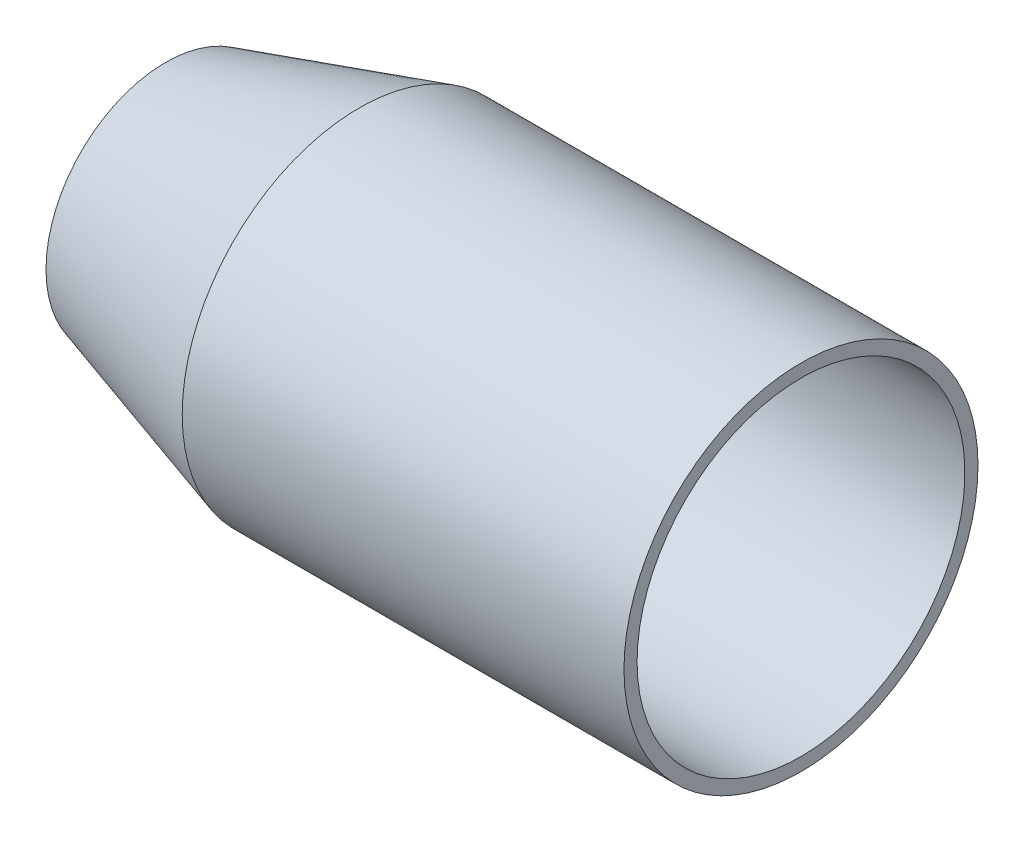
SolidWorks part; units mm, degrees
ref_plane "Front Plane" through (0, 0, 0) normal (0, 0, 1) x (1, 0, 0)
ref_plane "Top Plane" through (0, 0, 0) normal (0, 1, 0) x (1, 0, 0)
ref_plane "Right Plane" through (0, 0, 0) normal (1, 0, 0) x (0, 0, -1)
sketch "Sketch1" plane through (0, 0, 0) normal (0, 0, 1) x (1, 0, 0)
  line L0 (0, 0) -> (541.4119, 0) construction
  line L1 (266.7, 68.795) -> (266.7, 137.92)
  line L2 (266.7, 137.92) -> (239.01, 137.92)
  line L3 (239.01, 137.92) -> (239.01, 74.295)
  line L4 (239.01, 74.295) -> (81.28, 74.295)
  line L5 (239.01, 68.795) -> (82.0785, 68.795)
  line L6 (239.01, 68.795) -> (266.7, 68.795)
  line L7 (81.28, 74.295) -> (0, 50.1868)
  line L8 (82.0785, 68.795) -> (0, 44.45)
  line L9 (0, 50.1868) -> (0, 44.45)
  line L10 (239.01, 74.295) -> (266.7, 74.295)
  dimension "D2" = 27.69
  dimension "D3" = 74.295
  dimension "D4" = 185.42
  dimension "D5" = 266.7
  dimension "D6" = 5.5
  dimension "D7" = 5.5
  dimension "D1" = 44.45
revolve "Revolve1" add sketch "Sketch1" angle 360 about L0
sketch "Sketch3" plane through (266.7, 0, 0) normal (1, 0, 0) x (0, 0, -1)
  line L0 (0, 0) -> (0, 120.65) construction
  line L1 (0, 0) -> (-46.1708, 111.4661) construction
  circle A0 centre (0, 0) radius 120.65 construction
  dimension "D1" = 241.3
  dimension "D2" = 22.5
hole_wizard "1/16 (0.88) Diameter Hole1" [suppressed] positions "3DSketch2" profile "Sketch7" hole size "1/16" standard "ANSI Inch"
sketch3d "3DSketch2"
  point P0 (266.7, 111.4661, 46.1708)
sketch "Sketch7" plane through (266.7, 111.4661, 46.1708) normal (0, 1, 0) x (0, 0, -1)
  line L0 (0, 0) -> (0, 266.7)
  line L1 (0, 266.7) -> (11.176, 266.7)
  line L2 (11.176, 266.7) -> (11.176, 0)
  line L5 (11.176, 0) -> (0, 0)
  line L11 (0, -6.35) -> (0, 107.95) construction
  dimension "Thru Hole Dia." = 22.352
  dimension "Thru Hole Depth" = 266.7
pattern_circular "CirPattern1" [suppressed] count 8 over 360
equation "\"Wall Thickness\"= 5.5"
equation "\"D6@Sketch1\"=\"Wall Thickness\""
equation "\"Nozzle diameter\"= 3.5 * 25.4"
equation "\"D7@Sketch1\"=\"Wall Thickness\""
equation "\"D1@Sketch1\"=\"Nozzle diameter\"/2"
